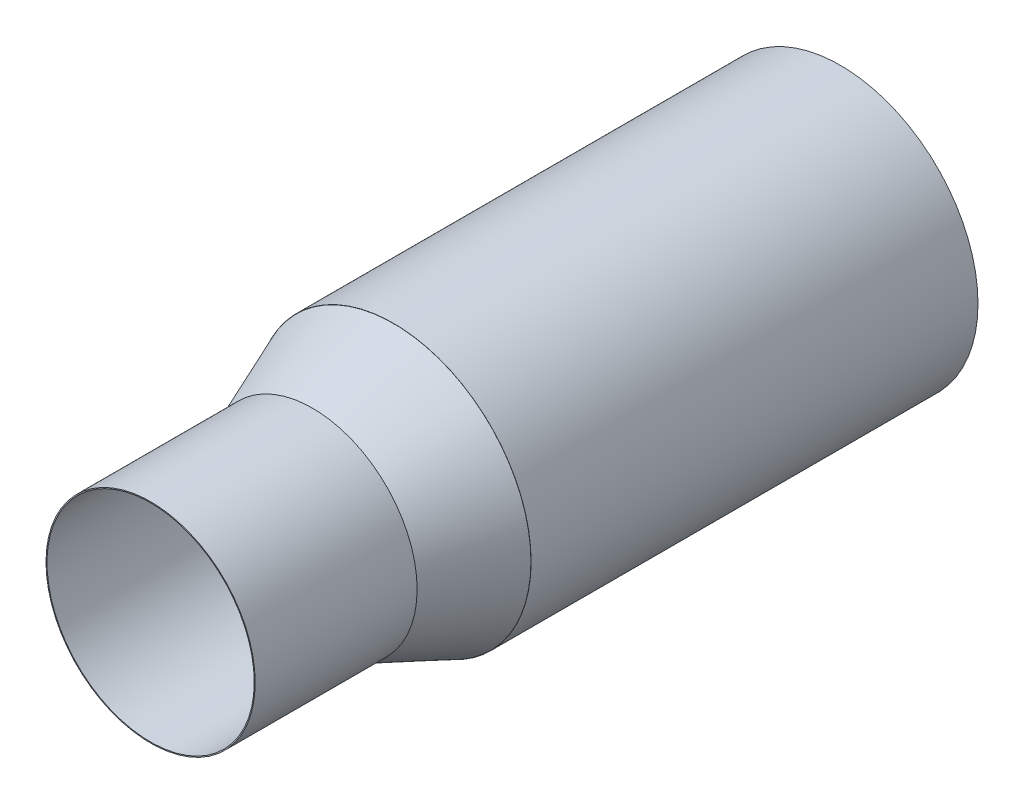
SolidWorks part; units mm, degrees
ref_plane "Front Plane" through (0, 0, 0) normal (0, 0, 1) x (1, 0, 0)
ref_plane "Top Plane" through (0, 0, 0) normal (0, 1, 0) x (1, 0, 0)
ref_plane "Right Plane" through (0, 0, 0) normal (1, 0, 0) x (0, 0, -1)
sketch "Sketch1" plane through (0, 0, 0) normal (0, 0, 1) x (1, 0, 0)
  line L0 (0, 0) -> (-20.1218, 11.3741) construction
  line L1 (0, 0) -> (19.9112, 11.7389) construction
  line L2 (0, 0) -> (0.2377, -23.114) construction
  circle A4 centre (0.1189, -11.557) radius 9.144
  circle A5 centre (9.9556, 5.8695) radius 9.144
  circle A6 centre (-10.0609, 5.687) radius 9.144
  circle A8 centre (0, 0) radius 21.59
  point P1 (2.188, 1.29)
  point P2 (-2.2112, 1.2499)
  point P6 (0.0261, -2.54)
  point P7 (9.9556, 5.8695)
  point P8 (-10.0609, 5.687)
  point P9 (0.1189, -11.557)
  dimension "D1" = 2.54
  dimension "D2" = 2.54
  dimension "D3" = 2.54
  dimension "D4" = 9.017
  dimension "D5" = 9.017
  dimension "D6" = 9.017
extrude "Boss-Extrude1" add sketch "Sketch1" along normal blind 70.1
sketch "Sketch2" plane through (0, 0, 70.1) normal (0, 0, 1) x (1, 0, 0)
  circle A0 centre (0, 0) radius 21.59
  circle A2 centre (0, 0) radius 16.4084
  circle A3 centre (0, 0) radius 16.256
  circle M4 centre (9.9556, 5.8695) radius 9.144
  circle M6 centre (0.1189, -11.557) radius 9.144
  circle M7 centre (-10.0609, 5.687) radius 9.144
extrude "Boss-Extrude2" add sketch "Sketch2" along normal blind 38.1 contours A3 A2 M7 | A3 A2 M4 M7 | A3 A2 M4 | A3 A2 M6 M4 | A3 A2 M6 | A3 A2 M7 M6
sketch "Sketch8" plane through (0, 0, 0) normal (1, 0, 0) x (0, 0, -1)
  line L0 (-126.1598, 0) -> (24.1508, 0) construction
  line L1 (-70.1, -0.6209) -> (-70.1, 31.6682) construction
  line L2 (-89.15, 16.4084) -> (-70.1, 16.4084) construction
  line L3 (-70.1, 16.4084) -> (-108.2, 16.4084) construction
  line L4 (-70.1, 21.5623) -> (-82.8, 16.4084)
  line L5 (-70.1, 21.5623) -> (-70.1, 16.4084)
  line L6 (-70.1, 16.4084) -> (-82.8, 16.4084)
  point P10 (-82.8, 16.4084)
  dimension "D1" = 12.7
revolve "Revolve3" add sketch "Sketch8" angle 360 about L0
sketch "Sketch14" [suppressed] plane through (0, 0, 0) normal (1, 0, 0) x (0, 0, -1)
  line L0 (-70.1, 21.59) -> (-61.3375, 66.04)
  line L3 (0, 21.59) -> (-70.1, 72.39) construction
  line L4 (0, 21.59) -> (-35.05, 72.39) construction
  line L5 (0, 21.59) -> (-70.1, 21.59) construction
  line L6 (-70.1, 21.59) -> (0, 72.39) construction
  line L7 (-61.3375, 66.04) -> (-35.05, 72.39)
  line L8 (-35.05, 72.39) -> (0, 72.39)
  line L9 (0, 72.39) -> (0, 46.99)
  line L10 (0, 46.99) -> (0, 21.59)
  line L11 (0, 21.59) -> (-70.1, 21.59)
  point P7 (-30.6688, 66.04)
  point P9 (-35.05, 46.99)
  point P10 (-57.4, 21.59)
  point P11 (-12.7, 21.59)
  point P12 (-70.1, 46.99)
  point P14 (0, 46.99)
  point P15 (-61.3375, 66.04)
  point P16 (-8.7625, 66.04)
  dimension "D3" = 12.7
  dimension "D1" = 6.35
  dimension "D2" = 50.8
  dimension "D4" = 12.7
extrude "Boss-Extrude4" [suppressed] add sketch "Sketch14" against normal blind 2.54 separate body
